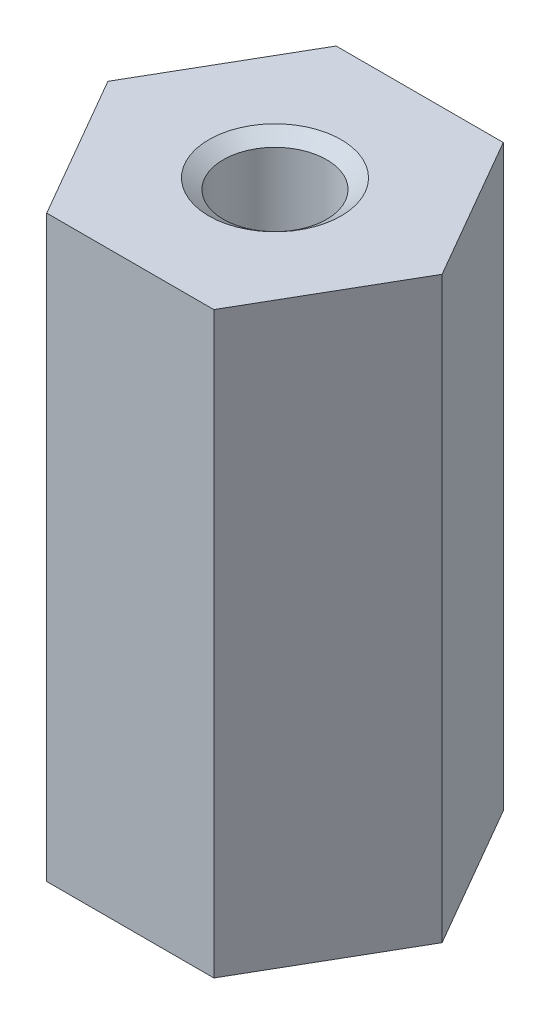
SolidWorks part; units mm, degrees
material "1,0501 (C35)"
ref_plane "Спереди" through (0, 0, 0) normal (0, 0, 1) x (1, 0, 0)
ref_plane "Сверху" through (0, 0, 0) normal (0, 1, 0) x (1, 0, 0)
ref_plane "Справа" through (0, 0, 0) normal (1, 0, 0) x (0, 0, -1)
sketch "Эскиз1" plane through (0, 0, 0) normal (0, 1, 0) x (1, 0, 0)
  line L1 (4.0415, 0) -> (2.0207, 3.5)
  line L2 (2.0207, 3.5) -> (-2.0207, 3.5)
  line L3 (-2.0207, 3.5) -> (-4.0415, 0)
  line L4 (-4.0415, 0) -> (-2.0207, -3.5)
  line L5 (-2.0207, -3.5) -> (2.0207, -3.5)
  line L6 (2.0207, -3.5) -> (4.0415, 0)
  circle A0 centre (0, 0) radius 3.5 construction
  dimension "D1" = 7
extrude "Бобышка-Вытянуть1" add sketch "Эскиз1" along normal blind 14
hole_wizard "Отверстие обработанное метчиком M3x0.51" positions "Эскиз3" profile "Эскиз2" tap size "M3x0.5" standard "Ansi (метрические)" end condition through all
sketch "Эскиз3" plane through (0, 14, 0) normal (0, 1, 0) x (-1, 0, 0)
  point P0 (0, 0)
sketch "Эскиз2" plane through (0, 14, 0) normal (1, 0, 0) x (0, 0, 1)
  line L0 (0, 0) -> (0, 14)
  line L1 (0, 14) -> (1.6, 14)
  line L2 (1.25, 13.7549) -> (1.25, 0.2451)
  line L3 (1.25, 0.2451) -> (1.6, 0)
  line L5 (1.6, 0) -> (0, 0)
  line L6 (-1.25, 0.2451) -> (-1.6, 0) construction
  line L7 (1.6, 14) -> (1.25, 13.7549)
  line L8 (-1.6, 14) -> (-1.25, 13.7549) construction
  line L11 (0, -6.35) -> (0, 107.95) construction
  dimension "Диаметр проходного сверла" = 2.5
  dimension "Глубина проходного сверла" = 14
  dimension "Диаметр передней зенковки" = 3.2
  dimension "Угол передней зенковки" = 110
  dimension "Диаметр задней зенковки" = 3.2
  dimension "Угол задней зенковки" = 110
cosmetic thread "Отверстие резьбы1" parameters "D2"=3
